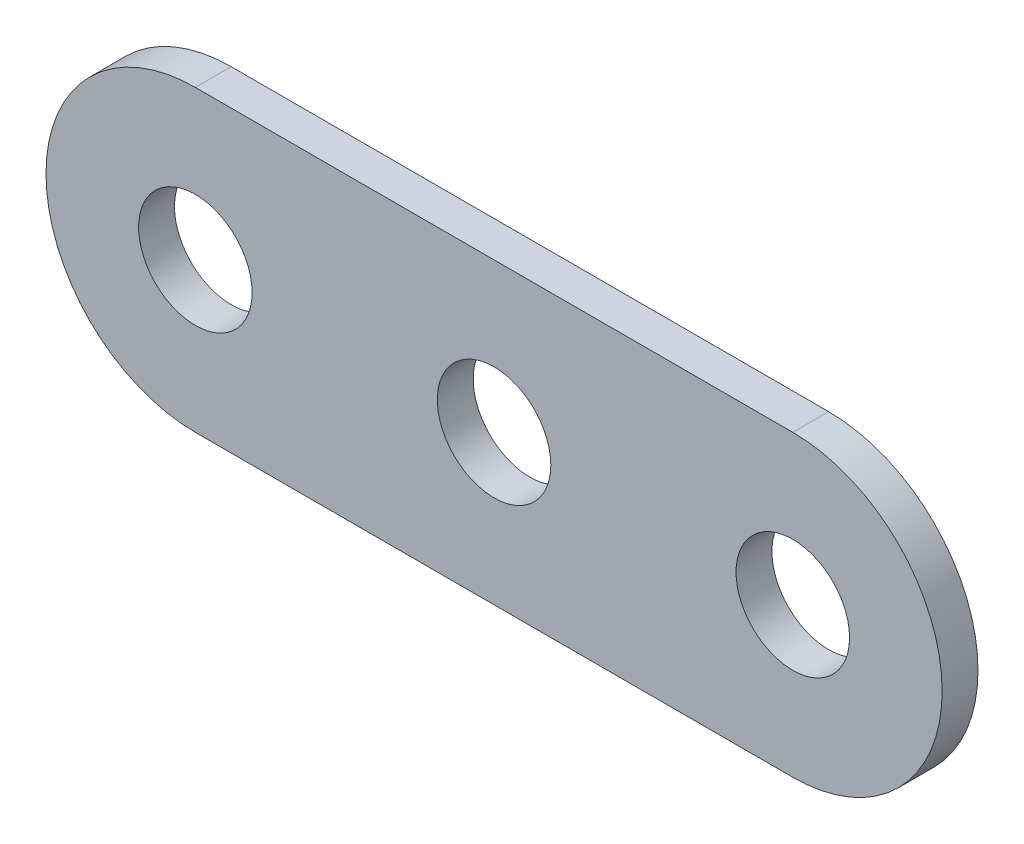
SolidWorks part; units mm, degrees
material "6061 Alloy"
ref_plane "Front Plane" through (0, 0, 0) normal (0, 0, 1) x (1, 0, 0)
ref_plane "Top Plane" through (0, 0, 0) normal (0, 1, 0) x (1, 0, 0)
ref_plane "Right Plane" through (0, 0, 0) normal (1, 0, 0) x (0, 0, -1)
sketch "Sketch1" plane through (0, 0, 0) normal (0, 0, 1) x (1, 0, 0)
  line L0 (-12.7, 0) -> (12.7, 0) construction
  line L1 (-12.7, -6.35) -> (12.7, -6.35)
  line L3 (-12.7, 6.35) -> (12.7, 6.35)
  arc A0 (12.7, 6.35) -> (12.7, -6.35) centre (12.7, 0) cw
  arc A1 (-12.7, 6.35) -> (-12.7, -6.35) centre (-12.7, 0) ccw
  dimension "D2" = 6.35
  dimension "D1" = 25.4
extrude "Extrude1" add sketch "Sketch1" along normal blind 1.524
sketch "Sketch2" plane through (0, 0, 1.524) normal (0, 0, 1) x (1, 0, 0)
  circle A0 centre (-12.7, 0) radius 2.413
  dimension "D1" = 4.826
extrude "Extrude2" cut sketch "Sketch2" against normal through all
pattern_linear "LPattern1" count 3 spacing 12.7 along (1, 0, 0) of "Extrude2"
